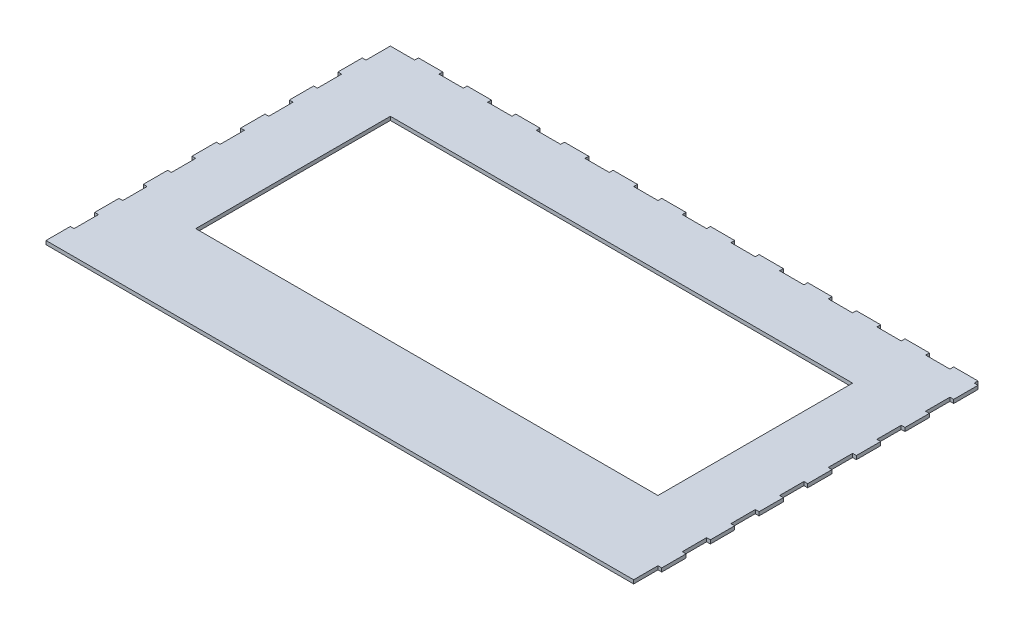
SolidWorks part; units mm, degrees
material "Acrílico (Impacto medio-alto)"
ref_plane "Alzado" through (0, 0, 0) normal (0, 0, 1) x (1, 0, 0)
ref_plane "Planta" through (0, 0, 0) normal (0, 1, 0) x (1, 0, 0)
ref_plane "Vista lateral" through (0, 0, 0) normal (1, 0, 0) x (0, 0, -1)
sketch "Croquis1" plane through (0, 0, 0) normal (0, 1, 0) x (1, 0, 0)
  line L0 (480, 280) -> (480, 283.1)
  line L1 (0, 0) -> (480, 0)
  line L2 (0, 0) -> (0, 280) construction
  line L3 (0, 280) -> (480, 280) construction
  line L4 (480, 0) -> (480, 280) construction
  line L5 (480, 283.1) -> (460, 283.1)
  line L6 (460, 283.1) -> (460, 280)
  line L7 (460, 280) -> (440, 280)
  line L8 (420, 280) -> (400, 280)
  line L9 (420, 283.1) -> (420, 280)
  line L10 (440, 283.1) -> (420, 283.1)
  line L11 (440, 280) -> (440, 283.1)
  line L12 (380, 280) -> (360, 280)
  line L13 (380, 283.1) -> (380, 280)
  line L14 (400, 283.1) -> (380, 283.1)
  line L15 (400, 280) -> (400, 283.1)
  line L16 (340, 280) -> (320, 280)
  line L17 (340, 283.1) -> (340, 280)
  line L18 (360, 283.1) -> (340, 283.1)
  line L19 (360, 280) -> (360, 283.1)
  line L20 (300, 280) -> (280, 280)
  line L21 (300, 283.1) -> (300, 280)
  line L22 (320, 283.1) -> (300, 283.1)
  line L23 (320, 280) -> (320, 283.1)
  line L24 (260, 280) -> (240, 280)
  line L25 (260, 283.1) -> (260, 280)
  line L26 (280, 283.1) -> (260, 283.1)
  line L27 (280, 280) -> (280, 283.1)
  line L28 (220, 280) -> (200, 280)
  line L29 (220, 283.1) -> (220, 280)
  line L30 (240, 283.1) -> (220, 283.1)
  line L31 (240, 280) -> (240, 283.1)
  line L32 (180, 280) -> (160, 280)
  line L33 (180, 283.1) -> (180, 280)
  line L34 (200, 283.1) -> (180, 283.1)
  line L35 (200, 280) -> (200, 283.1)
  line L36 (140, 280) -> (120, 280)
  line L37 (140, 283.1) -> (140, 280)
  line L38 (160, 283.1) -> (140, 283.1)
  line L39 (160, 280) -> (160, 283.1)
  line L40 (100, 280) -> (80, 280)
  line L41 (100, 283.1) -> (100, 280)
  line L42 (120, 283.1) -> (100, 283.1)
  line L43 (120, 280) -> (120, 283.1)
  line L44 (60, 280) -> (40, 280)
  line L45 (60, 283.1) -> (60, 280)
  line L46 (80, 283.1) -> (60, 283.1)
  line L47 (80, 280) -> (80, 283.1)
  line L48 (20, 280) -> (0, 280)
  line L49 (20, 283.1) -> (20, 280)
  line L50 (40, 283.1) -> (20, 283.1)
  line L51 (40, 280) -> (40, 283.1)
  line L52 (480, 280) -> (483.1, 280)
  line L53 (483.1, 280) -> (483.1, 260)
  line L54 (483.1, 260) -> (480, 260)
  line L55 (480, 260) -> (480, 240)
  line L56 (480, 240) -> (483.1, 240)
  line L57 (483.1, 240) -> (483.1, 220)
  line L58 (483.1, 220) -> (480, 220)
  line L59 (480, 220) -> (480, 200)
  line L60 (480, 200) -> (483.1, 200)
  line L61 (483.1, 200) -> (483.1, 180)
  line L62 (483.1, 180) -> (480, 180)
  line L63 (480, 180) -> (480, 160)
  line L64 (480, 160) -> (483.1, 160)
  line L65 (483.1, 160) -> (483.1, 140)
  line L66 (483.1, 140) -> (480, 140)
  line L67 (480, 140) -> (480, 120)
  line L68 (480, 120) -> (483.1, 120)
  line L69 (483.1, 120) -> (483.1, 100)
  line L70 (483.1, 100) -> (480, 100)
  line L71 (480, 100) -> (480, 80)
  line L72 (480, 80) -> (483.1, 80)
  line L73 (483.1, 80) -> (483.1, 60)
  line L74 (483.1, 60) -> (480, 60)
  line L75 (480, 60) -> (480, 40)
  line L76 (480, 40) -> (483.1, 40)
  line L77 (483.1, 40) -> (483.1, 20)
  line L78 (483.1, 20) -> (480, 20)
  line L79 (480, 20) -> (480, 0)
  line L80 (0, 0) -> (-3.1, 0)
  line L81 (-3.1, 0) -> (-3.1, 20)
  line L82 (-3.1, 20) -> (0, 20)
  line L83 (0, 20) -> (0, 40)
  line L84 (-3.1, 40) -> (-3.1, 60)
  line L85 (-3.1, 60) -> (0, 60)
  line L86 (0, 60) -> (0, 80)
  line L87 (0, 40) -> (-3.1, 40)
  line L88 (-3.1, 80) -> (-3.1, 100)
  line L89 (-3.1, 100) -> (0, 100)
  line L90 (0, 100) -> (0, 120)
  line L91 (0, 80) -> (-3.1, 80)
  line L92 (-3.1, 120) -> (-3.1, 140)
  line L93 (-3.1, 140) -> (0, 140)
  line L94 (0, 140) -> (0, 160)
  line L95 (0, 120) -> (-3.1, 120)
  line L96 (-3.1, 160) -> (-3.1, 180)
  line L97 (-3.1, 180) -> (0, 180)
  line L98 (0, 180) -> (0, 200)
  line L99 (0, 160) -> (-3.1, 160)
  line L100 (-3.1, 200) -> (-3.1, 220)
  line L101 (-3.1, 220) -> (0, 220)
  line L102 (0, 220) -> (0, 240)
  line L103 (0, 200) -> (-3.1, 200)
  line L104 (-3.1, 240) -> (-3.1, 260)
  line L105 (-3.1, 260) -> (0, 260)
  line L106 (0, 260) -> (0, 280)
  line L107 (0, 240) -> (-3.1, 240)
  dimension "D1" = 12
  dimension "D2" = 7
  dimension "D3" = 7
extrude "Saliente-Extruir1" add sketch "Croquis1" along normal blind 3
sketch "Croquis2" plane through (0, 3, 0) normal (0, 1, 0) x (1, 0, 0)
  line L0 (480, 280) -> (430, 280) construction
  line L1 (430, 280) -> (430, 230) construction
  line L3 (430, 230) -> (50, 230)
  line L4 (430, 230) -> (430, 70)
  line L5 (430, 70) -> (50, 70)
  line L6 (50, 230) -> (50, 70)
extrude "Cortar-Extruir1" cut sketch "Croquis2" against normal blind 3
